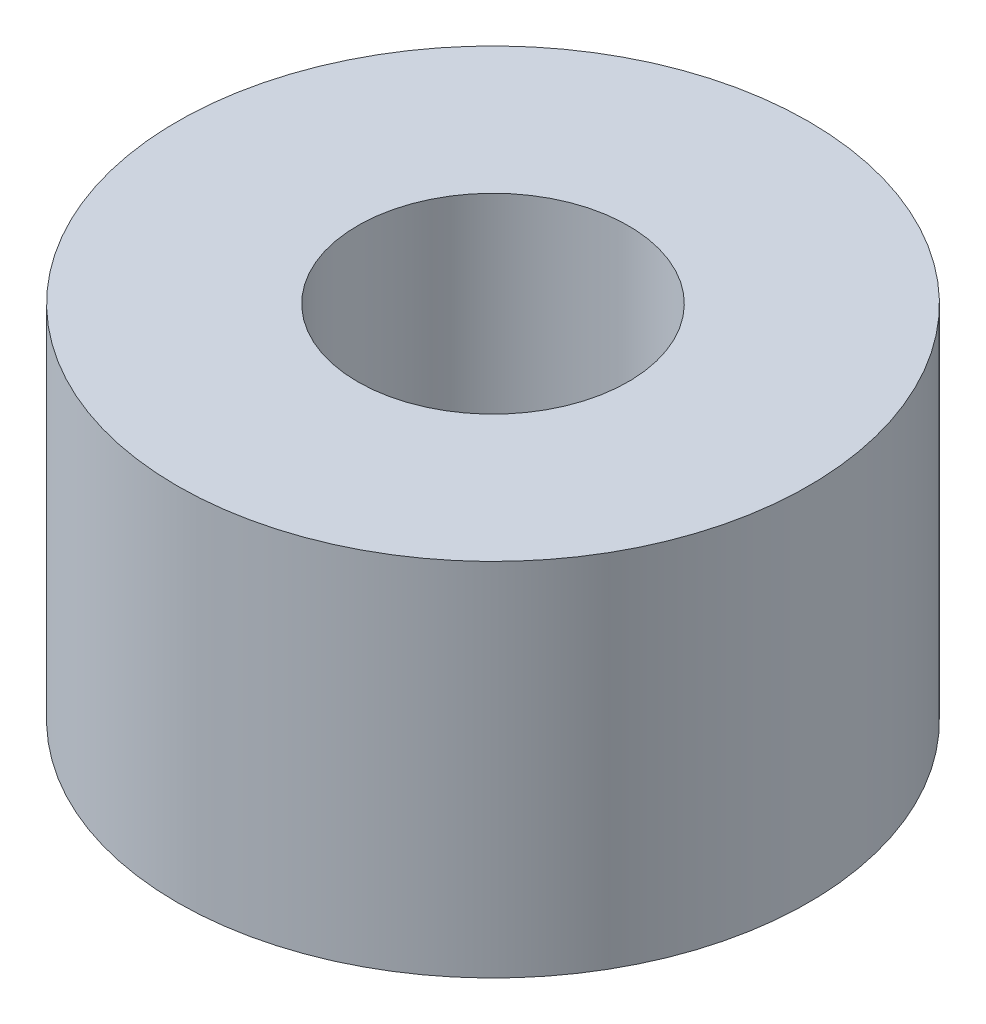
SolidWorks part; units mm, degrees
ref_plane "前视基准面" through (0, 0, 0) normal (0, 0, 1) x (1, 0, 0)
ref_plane "上视基准面" through (0, 0, 0) normal (0, 1, 0) x (1, 0, 0)
ref_plane "右视基准面" through (0, 0, 0) normal (1, 0, 0) x (0, 0, -1)
sketch "草图1" plane through (0, 0, 0) normal (0, 1, 0) x (1, 0, 0)
  circle A0 centre (0, 0) radius 3.5
  circle A1 centre (0, 0) radius 1.5
  dimension "D1" = 3
  dimension "D2" = 7
extrude "凸台-拉伸1" add sketch "草图1" along normal blind 4
